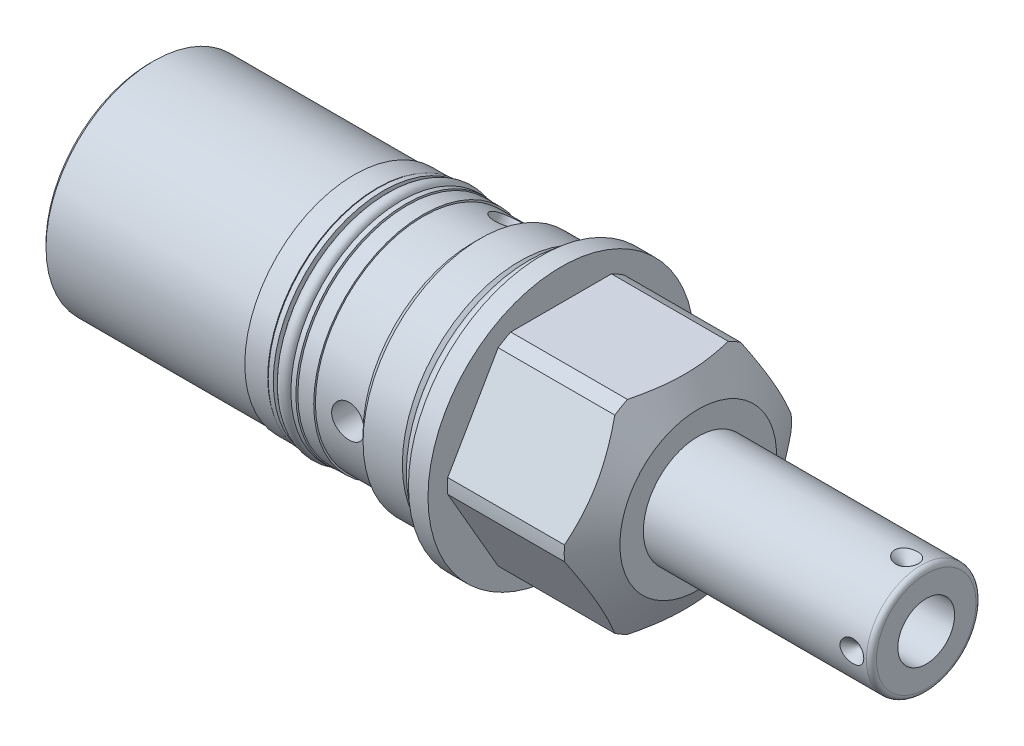
SolidWorks part; units mm, degrees
material "Alloy Steel"
ref_plane "Front Plane" through (0, 0, 0) normal (0, 0, 1) x (1, 0, 0)
ref_plane "Top Plane" through (0, 0, 0) normal (0, 1, 0) x (1, 0, 0)
ref_plane "Right Plane" through (0, 0, 0) normal (1, 0, 0) x (0, 0, -1)
ref_plane "Plane1" through (0, 0, 0) normal (1, 0, 0) x (0, 0, -1)
sketch "Sketch1" plane through (0, 0, 0) normal (1, 0, 0) x (0, 0, -1)
  circle A0 centre (0, 0) radius 26.9875
  dimension "D1" = 53.975
extrude "Extrude1" add sketch "Sketch1" along normal blind 31.75 and the other way blind 79.375
ref_plane "Plane2" through (0, 0, 0) normal (1, 0, 0) x (0, 0, -1)
sketch "Sketch2" plane through (0, 0, 0) normal (1, 0, 0) x (0, 0, -1)
  circle A0 centre (0, 0) radius 23.8125
  circle A1 centre (0, 0) radius 26.9875 construction
  circle A2 centre (0, 0) radius 26.9875
  dimension "D1" = 47.625
extrude "Cut-Extrude1" cut sketch "Sketch2" against normal up to next
ref_plane "Plane3" through (0, 0, 0) normal (0, 0, 1) x (1, 0, 0)
sketch "Sketch3" plane through (0, 0, 0) normal (0, 0, 1) x (1, 0, 0)
  line L0 (25.3342, 26.9875) -> (31.75, 15.875)
  line L1 (-8.1458, 0) -> (17.0188, 0) construction
  line L2 (31.75, 15.875) -> (31.75, 26.9875)
  line L3 (31.75, 26.9875) -> (25.3342, 26.9875)
  line L4 (31.75, 26.9875) -> (0, 26.9875) construction
  dimension "D1" = 31.75
  dimension "D2" = 30
revolve "Cut-Revolve1" cut sketch "Sketch3" angle 360 about L1
ref_plane "Plane5" through (3.175, 0, 0) normal (-1, 0, 0) x (0, 0, 1)
sketch "Sketch5" plane through (3.175, 0, 0) normal (-1, 0, 0) x (0, 0, 1)
  line L0 (-11.9151, 20.6375) -> (11.9151, 20.6375)
  line L1 (11.9151, 20.6375) -> (23.8301, 0)
  line L2 (23.8301, 0) -> (11.9151, -20.6375)
  line L3 (11.9151, -20.6375) -> (-11.9151, -20.6375)
  line L4 (-11.9151, -20.6375) -> (-23.8301, 0)
  line L5 (-23.8301, 0) -> (-11.9151, 20.6375)
  line L6 (0, 0) -> (18.7904, 0) construction
  line L7 (0, 0) -> (11.9151, 20.6375) construction
  line L8 (0, 0) -> (-11.9151, 20.6375) construction
  circle A0 centre (0, 0) radius 26.9875 construction
  circle A1 centre (0, 0) radius 26.9875
  dimension "D1" = 41.275
  dimension "D2" = 120
  dimension "D3" = 60
extrude "Cut-Extrude3" cut sketch "Sketch5" against normal up to next from offset 0.7874 offset against normal yes
ref_plane "Plane7" through (3.175, 0, 0) normal (-1, 0, 0) x (0, 0, 1)
sketch "Sketch7" plane through (3.9624, 0, 0) normal (-1, 0, 0) x (0, 0, 1)
  circle A0 centre (0, 0) radius 23.0251
  circle A1 centre (0, 0) radius 26.9875 construction
  circle A2 centre (0, 0) radius 26.9875
  dimension "D1" = 46.0502
extrude "Cut-Extrude5" cut sketch "Sketch7" against normal up to next
ref_plane "Plane9" through (0, 0, 0) normal (0, 0, 1) x (1, 0, 0)
sketch "Sketch9" plane through (0, 0, 0) normal (0, 0, 1) x (1, 0, 0)
  line L0 (0, 23.8125) -> (0, 22.3012)
  line L1 (0, 22.3012) -> (-2.8956, 22.3012)
  line L2 (-2.8956, 22.3012) -> (-4.4069, 23.8125)
  line L3 (-4.4206, 0) -> (0.2105, 0) construction
  line L4 (0, 23.8125) -> (-4.4069, 23.8125)
  line L5 (0, 23.8125) -> (-79.375, 23.8125) construction
  line L6 (0, 26.9875) -> (0, -26.9875) construction
  dimension "D1" = 2.8956
  dimension "D2" = 45
  dimension "D3" = 44.6024
revolve "Cut-Revolve3" cut sketch "Sketch9" angle 360 about L3
ref_plane "Plane10" through (0, 0, 0) normal (0, 0, 1) x (1, 0, 0)
sketch "Sketch10" plane through (0, 0, 0) normal (0, 0, 1) x (1, 0, 0)
  line L0 (-12.3698, 23.8125) -> (-13.9954, 22.1869)
  line L1 (-13.9954, 22.1869) -> (-79.375, 22.1869)
  line L2 (-55.947, 0) -> (-8.6516, 0) construction
  line L4 (-79.375, 23.8125) -> (-79.375, 22.1869)
  line L5 (-4.4069, 23.8125) -> (-4.4069, -23.8125) construction
  line L6 (-4.4069, 23.8125) -> (-79.375, 23.8125) construction
  line L7 (-12.3698, 23.8125) -> (-79.375, 23.8125)
  dimension "D1" = 44.3738
  dimension "D2" = 45
  dimension "D3" = 7.9629
revolve "Cut-Revolve4" cut sketch "Sketch10" angle 360 about L2
ref_plane "Plane12" through (0, 0, 0) normal (0, 0, 1) x (1, 0, 0)
sketch "Sketch12" plane through (0, 0, 0) normal (0, 0, 1) x (1, 0, 0)
  line L0 (-33.3248, 22.1869) -> (-33.3248, 20.1549)
  line L1 (-33.3248, 20.1549) -> (-27.2161, 20.1549)
  line L2 (-27.2161, 20.1549) -> (-27.2161, 22.1869)
  line L3 (-31.7506, 0) -> (-25.0311, 0) construction
  line L4 (-33.3248, 22.1869) -> (-27.2161, 22.1869)
  line L5 (-13.9954, 22.1869) -> (-79.375, 22.1869) construction
  line L6 (-79.375, 22.1869) -> (-79.375, -22.1869) construction
  dimension "D1" = 6.1087
  dimension "D2" = 40.3098
  dimension "D3" = 46.0502
revolve "Cut-Revolve6" cut sketch "Sketch12" angle 360 about L3
ref_plane "Plane14" through (0, 0, 0) normal (0, 0, 1) x (0, -1, 0)
sketch "Sketch14" plane through (0, 0, 0) normal (0, 0, 1) x (0, -1, 0)
  line L0 (22.1869, -79.375) -> (21.844, -79.375)
  line L1 (21.844, -79.375) -> (21.844, -37.973)
  line L2 (21.844, -37.973) -> (22.1869, -37.973)
  line L3 (22.1869, -37.973) -> (22.1869, -79.375)
  line L4 (22.1869, -13.9954) -> (21.844, -13.9954)
  line L5 (21.844, -13.9954) -> (21.844, -24.003)
  line L6 (21.844, -24.003) -> (22.1869, -24.003)
  line L7 (22.1869, -24.003) -> (22.1869, -13.9954)
  line L8 (0, -55.866) -> (0, -10.3518) construction
  line L9 (22.1869, -79.375) -> (22.1869, -33.3248) construction
  line L10 (22.1869, -27.2161) -> (22.1869, -13.9954) construction
  line L11 (-22.1869, -79.375) -> (22.1869, -79.375) construction
  dimension "D1" = 13.97
  dimension "D2" = 43.688
  dimension "D3" = 41.402
  dimension "D4" = 10.0076
revolve "Cut-Revolve8" cut sketch "Sketch14" angle 360 about L8
ref_plane "Plane15" through (0, 0, 0) normal (0, 0, 1) x (0, -1, 0)
sketch "Sketch15" plane through (0, 0, 0) normal (0, 0, 1) x (0, -1, 0)
  line L0 (0, -3.0937) -> (0, 0.1473) construction
  line L1 (-26.9875, 0) -> (26.9875, 0) construction
  circle A0 centre (23.7998, -1.4986) radius 1.4986
  dimension "D1" = 2.9972
  dimension "D2" = 1.4986
  dimension "D3" = 47.5996
revolve "Revolve1" add sketch "Sketch15" angle 360 about L0
ref_plane "Plane16" through (0, 0, 0) normal (0, 0, 1) x (0, -1, 0)
sketch "Sketch16" plane through (0, 0, 0) normal (0, 0, 1) x (0, -1, 0)
  line L0 (20.1549, -27.4701) -> (22.3393, -27.4701)
  line L1 (22.3393, -27.4701) -> (22.3393, -28.4861)
  line L2 (22.3393, -28.4861) -> (20.1549, -28.4861)
  line L3 (20.1549, -28.4861) -> (20.1549, -27.4701)
  line L4 (20.1549, -33.0708) -> (22.3393, -33.0708)
  line L5 (22.3393, -33.0708) -> (22.3393, -32.0548)
  line L6 (22.3393, -32.0548) -> (20.1549, -32.0548)
  line L7 (20.1549, -32.0548) -> (20.1549, -33.0708)
  line L8 (0, -31.4712) -> (0, -25.3105) construction
  line L9 (-22.1869, -27.2161) -> (22.1869, -27.2161) construction
  line L10 (22.1869, -33.3248) -> (-22.1869, -33.3248) construction
  line L11 (20.1549, -33.3248) -> (20.1549, -27.2161) construction
  dimension "D1" = 1.016
  dimension "D3" = 44.6786
  dimension "D4" = 0.254
  dimension "D5" = 0.254
revolve "Revolve2" add sketch "Sketch16" angle 360 about L8
ref_plane "Plane17" through (0, 0, 0) normal (0, 0, 1) x (0, -1, 0)
sketch "Sketch17" plane through (0, 0, 0) normal (0, 0, 1) x (0, -1, 0)
  line L0 (0, -31.7506) -> (0, -25.0311) construction
  line L1 (22.3393, -32.0548) -> (-22.3393, -32.0548) construction
  circle A0 centre (21.463, -30.2705) radius 1.3081
  point P0 (9.8298, -25.3365)
  point P1 (9.8298, -31.4452)
  dimension "D1" = 2.6162
  dimension "D2" = 42.926
  dimension "D3" = 1.7843
revolve "Revolve3" add sketch "Sketch17" angle 360 about L0
ref_plane "Plane18" through (0, 0, 0) normal (0, 0, 1) x (0, -1, 0)
sketch "S2D0001" plane through (0, 0, 0) normal (0, 0, 1) x (0, -1, 0)
  line L0 (0, 31.75) -> (-11.1125, 31.75)
  line L1 (-11.1125, 31.75) -> (-11.1125, 76.962)
  line L2 (-10.0965, 77.978) -> (0, 77.978)
  line L3 (0, 77.978) -> (0, 31.75)
  line L4 (0, 7.2658) -> (0, 37.3443) construction
  line L5 (15.875, 31.75) -> (-15.875, 31.75) construction
  line L6 (-26.9875, 0) -> (26.9875, 0) construction
  arc A0 (-10.0965, 77.978) -> (-11.1125, 76.962) centre (-10.0965, 76.962) ccw
  dimension "D2" = 1.016
  dimension "D1" = 22.225
  dimension "D3" = 77.978
revolve "Revolve4" add sketch "S2D0001" angle 360 about L4
ref_plane "Plane19" through (36.322, -2.8067, 0) normal (0, 0, 1) x (0, -1, 0)
sketch "Sketch19" plane through (36.322, -2.8067, 0) normal (0, 0, 1) x (0, -1, 0)
  line L0 (2.9464, 41.656) -> (2.9464, 24.638)
  line L1 (2.9464, 24.638) -> (-2.8067, 21.1812)
  line L2 (2.9464, 41.656) -> (-2.8067, 41.656)
  line L3 (-2.8067, 41.656) -> (-2.8067, 21.1812)
  line L4 (-2.8067, -18.6227) -> (-2.8067, 0.5923) construction
  line L5 (7.2898, 41.656) -> (-12.9032, 41.656) construction
  dimension "D1" = 11.5062
  dimension "D2" = 17.018
  dimension "D3" = 59
revolve "Cut-Revolve9" cut sketch "Sketch19" angle 360 about L4
ref_plane "Plane20" through (32.3596, 0, -5.5562) normal (0, 1, 0) x (1, 0, 0)
sketch "S2D0002" plane through (32.3596, 0, -5.5562) normal (0, 1, 0) x (1, 0, 0)
  line L0 (41.656, 5.5562) -> (44.069, 5.5562)
  line L1 (44.069, 5.5562) -> (41.656, 3.1433)
  line L2 (41.656, 5.5562) -> (41.656, 3.1433)
  line L3 (41.656, -3.3652) -> (41.656, 0.0794) construction
  line L4 (44.6024, 5.5562) -> (-0.6096, 5.5562) construction
  line L5 (45.6184, -15.6527) -> (45.6184, 4.5402) construction
  dimension "D1" = 3.9624
  dimension "D2" = 45
  dimension "D3" = 4.826
revolve "Cut-Revolve10" cut sketch "S2D0002" angle 360 about L3
pattern_circular "CirPattern1" count 4 over 360 about axis through (7.2658, 0, 0) along (-1, 0, 0) of "Cut-Revolve10"
chamfer "Chamfer1" distance 0.762 angle 45 1 edges at (-79.375, 0, 21.844)
sketch "Sketch23" plane through (0, 0, 0) normal (0, 0, 1) x (1, 0, 0)
  line L0 (-79.375, 21.082) -> (-79.375, -21.082) construction
  circle A0 centre (-17.399, 0) radius 3.3147
  dimension "D1" = 6.6294
  dimension "D2" = 61.976
extrude "Cut-Extrude7" cut sketch "Sketch23" along normal through all
sketch "Sketch26" plane through (-79.375, 0, 0) normal (-1, 0, 0) x (0, 0, 1)
  circle A0 centre (0, 0) radius 3.1369
  dimension "D1" = 6.2738
extrude "Cut-Extrude8" cut sketch "Sketch26" against normal blind 0.762
sketch "Sketch27" plane through (-79.375, 0, 0) normal (-1, 0, 0) x (0, 0, 1)
  circle A0 centre (0, 0) radius 17.7927
extrude "Extrude2" add sketch "Sketch27" along normal blind 0.508
sketch "Sketch28" plane through (-79.883, 0, 0) normal (-1, 0, 0) x (0, 0, 1)
  circle A0 centre (0, 0) radius 3.1369
extrude "Cut-Extrude9" cut sketch "Sketch28" against normal blind 0.508
pattern_circular "CirPattern2" count 3 over 360 about axis through (7.2658, 0, 0) along (-1, 0, 0) of "Cut-Extrude7"
